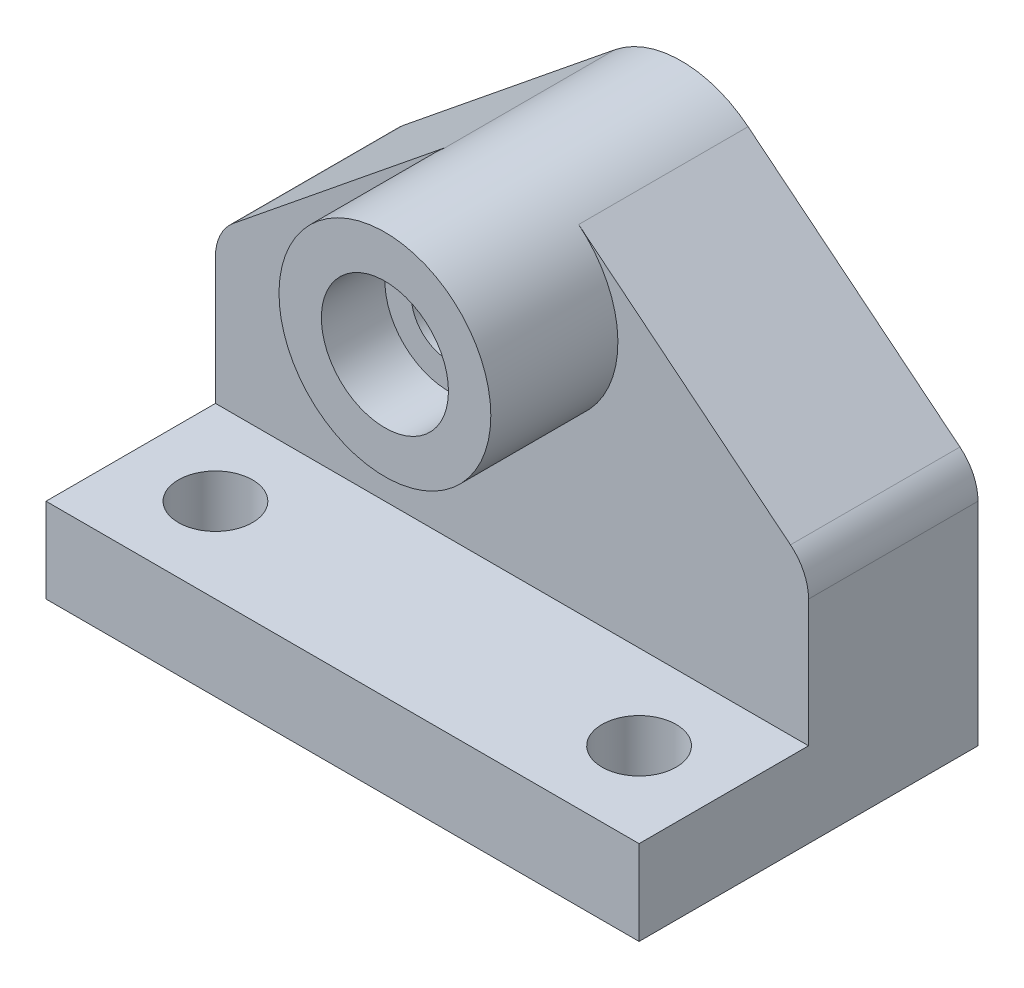
SolidWorks part; units mm, degrees
ref_plane "Front Plane" through (0, 0, 0) normal (0, 0, 1) x (1, 0, 0)
ref_plane "Top Plane" through (0, 0, 0) normal (0, 1, 0) x (1, 0, 0)
ref_plane "Right Plane" through (0, 0, 0) normal (1, 0, 0) x (0, 0, -1)
sketch "Sketch1" plane through (0, 0, 0) normal (0, 0, 1) x (1, 0, 0)
  line L0 (4.2688, 58.9487) -> (54.2688, 99.4301)
  line L1 (0, 0) -> (140, 0)
  line L2 (0, 0) -> (0, 50)
  line L4 (140, 0) -> (140, 50)
  line L5 (135.7312, 58.9487) -> (85.7312, 99.4301)
  arc A0 (0, 50) -> (4.2688, 58.9487) centre (11.5139, 50) cw
  arc A1 (140, 50) -> (135.7312, 58.9487) centre (128.4861, 50) ccw
  circle A2 centre (70, 80) radius 25
  dimension "D4" = 50
  dimension "D1" = 140
  dimension "D2" = 50
  dimension "D3" = 80
  dimension "D5" = 70
  dimension "D6" = 50
  dimension "D7" = 50
  dimension "D8" = 50
extrude "Boss-Extrude1" add sketch "Sketch1" along normal blind 80 contours A2 L0 A0 L2 L1 L4 A1 L5
sketch "Sketch2" plane through (0, 0, 0) normal (0, 0, -1) x (-1, 0, 0)
  circle A0 centre (-70, 80) radius 25
  dimension "D1" = 50
extrude "Boss-Extrude2" add sketch "Sketch2" against normal blind 40
sketch "Sketch3" plane through (0, 0, 80) normal (0, 0, 1) x (1, 0, 0)
  line L0 (45, 80) -> (45, 118.1278)
  line L1 (45, 118.1278) -> (112.483, 118.1278)
  line L2 (95, 80) -> (95, 118.1278)
  line L3 (45, 80) -> (95, 80)
  arc A0 (54.2688, 99.4301) -> (85.7312, 99.4301) centre (70, 80) ccw construction
  arc M1 (85.7312, 99.4301) -> (54.2688, 99.4301) centre (70, 80) cw
  line M2 (54.2688, 99.4301) -> (4.2688, 58.9487)
  line M8 (135.7312, 58.9487) -> (85.7312, 99.4301)
  dimension "D1" = 67.483
  dimension "D2" = 38.1278
  dimension "D3" = 38.1278
  dimension "D4" = 62.8787
extrude "Cut-Extrude2" cut sketch "Sketch3" against normal blind 40 contours L3 L2 L1 L0 M1 M8 M2 | L0 M1 M2 | L2 M1 M8
sketch "Sketch4" plane through (0, 0, 0) normal (0, -1, 0) x (1, 0, 0)
  point P0 (20, 60)
  point P1 (120, 60)
  dimension "D1" = 20
  dimension "D2" = 20
  dimension "D3" = 20
  dimension "D4" = 20
sketch "Sketch6" plane through (0, 0, 0) normal (0, -1, 0) x (-1, 0, 0)
  point P0 (-20, -20)
  point P1 (-120, -20)
  dimension "D1" = 20
  dimension "D2" = 20
  dimension "D3" = 20
  dimension "D4" = 20
hole_wizard "M20 Tapped Hole2" positions "3DSketch2" profile "Sketch7" tap size "M20" standard "ISO"
sketch3d "3DSketch2"
  point P0 (20, 0, 20)
  point P3 (120, 0, 20)
sketch "Sketch7" plane through (20, 0, 20) normal (1, 0, 0) x (0, 0, -1)
  line L0 (0, 0) -> (0, 35.2575)
  line L1 (0, 35.2575) -> (8.75, 30)
  line L2 (8.75, 30) -> (8.75, 0)
  line L5 (8.75, 0) -> (0, 0)
  line L10 (0, 35.2575) -> (-8.75, 30) construction
  line L11 (0, -6.35) -> (0, 107.95) construction
  dimension "Tap Drill Dia." = 17.5
  dimension "Tap Drill Depth" = 30
  dimension "Drill Angle" = 118
cosmetic thread "Hole Thread3" parameters "D1"=30, "D2"=20
cosmetic thread "Hole Thread4" parameters "D1"=30, "D2"=20
ref_plane "Plane1" through (0, 20, 0) normal (0, 1, 0) x (1, 0, 0)
sketch "Sketch9" plane through (0, 20, 0) normal (0, 1, 0) x (1, 0, 0)
  line L1 (0, -80) -> (140, -80)
  line L2 (0, -80) -> (0, -40)
  line L3 (0, -40) -> (140, -40)
  line L4 (140, -80) -> (140, -40)
  dimension "D1" = 40
extrude "Cut-Extrude3" cut sketch "Sketch9" along normal blind 110
sketch "Sketch12" plane through (0, 20, 0) normal (0, 1, 0) x (1, 0, 0)
  point P0 (20, -60)
  point P1 (120, -60)
  dimension "D1" = 20
  dimension "D2" = 20
  dimension "D3" = 20
  dimension "D4" = 20
hole_wizard "M20 Tapped Hole3" positions "3DSketch3" profile "Sketch13" tap size "M20" standard "ISO"
sketch3d "3DSketch3"
  point P0 (20, 20, 60)
  point P3 (120, 20, 60)
sketch "Sketch13" plane through (20, 20, 60) normal (1, 0, 0) x (0, 0, 1)
  line L0 (0, 0) -> (0, 42.7575)
  line L1 (0, 42.7575) -> (8.75, 37.5)
  line L2 (8.75, 37.5) -> (8.75, 0)
  line L5 (8.75, 0) -> (0, 0)
  line L10 (0, 42.7575) -> (-8.75, 37.5) construction
  line L11 (0, -6.35) -> (0, 107.95) construction
  dimension "Tap Drill Dia." = 17.5
  dimension "Tap Drill Depth" = 37.5
  dimension "Drill Angle" = 118
cosmetic thread "Hole Thread5" parameters "D1"=20, "D2"=20
cosmetic thread "Hole Thread6" parameters "D1"=20, "D2"=20
sketch "Sketch14" plane through (0, 0, 40) normal (0, 0, 1) x (1, 0, 0)
  circle A0 centre (70, 80) radius 25
  circle A1 centre (70, 80) radius 15
  dimension "D1" = 50
  dimension "D2" = 30
extrude "Boss-Extrude3" add sketch "Sketch14" along normal blind 30
sketch "Sketch15" plane through (0, 0, 40) normal (0, 0, 1) x (1, 0, 0)
  circle A0 centre (70, 80) radius 15
  dimension "D1" = 30
extrude "Boss-Extrude4" add sketch "Sketch15" along normal blind 30
sketch "Sketch16" plane through (0, 0, 70) normal (0, 0, 1) x (1, 0, 0)
  circle A0 centre (70, 80) radius 15
  dimension "D1" = 30
extrude "Cut-Extrude4" cut sketch "Sketch16" against normal blind 15
sketch "Sketch17" plane through (0, 0, 55) normal (0, 0, 1) x (1, 0, 0)
  point P0 (70, 80)
hole_wizard "M20 Tapped Hole4" positions "3DSketch5" profile "Sketch19" tap size "M20" standard "ISO"
sketch3d "3DSketch5"
  point P0 (70, 80, 55)
sketch "Sketch19" plane through (70, 80, 55) normal (1, 0, 0) x (0, -1, 0)
  line L0 (0, 0) -> (0, 65.2575)
  line L1 (0, 65.2575) -> (8.75, 60)
  line L2 (8.75, 60) -> (8.75, 0)
  line L5 (8.75, 0) -> (0, 0)
  line L10 (0, 65.2575) -> (-8.75, 60) construction
  line L11 (0, -6.35) -> (0, 107.95) construction
  dimension "Tap Drill Dia." = 17.5
  dimension "Tap Drill Depth" = 60
  dimension "Drill Angle" = 118
cosmetic thread "Hole Thread7" parameters "D1"=55, "D2"=20
